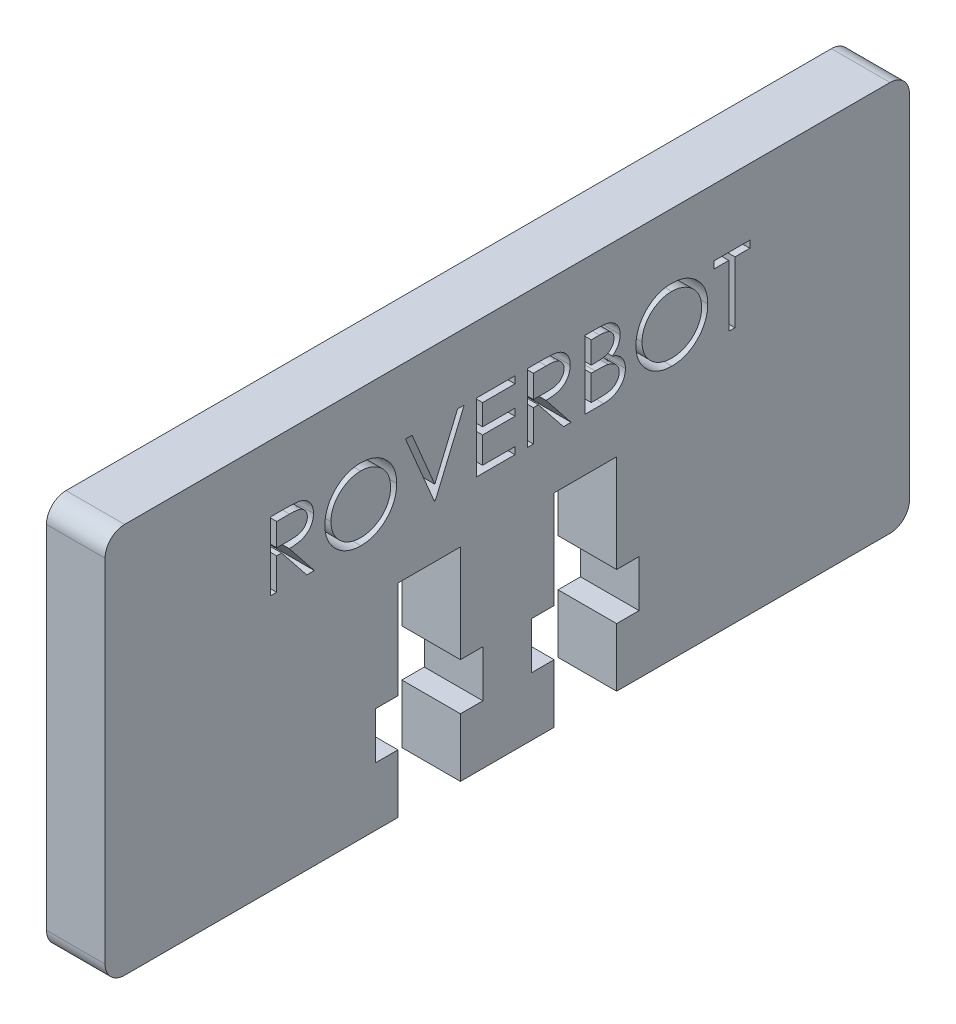
SolidWorks part; units mm, degrees
material "Beech"
ref_plane "Front Plane" through (0, 0, 0) normal (0, 0, 1) x (1, 0, 0)
ref_plane "Top Plane" through (0, 0, 0) normal (0, 1, 0) x (1, 0, 0)
ref_plane "Right Plane" through (0, 0, 0) normal (1, 0, 0) x (0, 0, -1)
sketch "Sketch1" plane through (0, 0, 0) normal (1, 0, 0) x (0, 0, -1)
  line L0 (-4, 0) -> (4, 0) construction
  line L1 (-5.6, 0) -> (-5.6, 3)
  line L2 (-5.6, 3) -> (-6.75, 3)
  line L3 (-6.75, 3) -> (-6.75, 5.4)
  line L4 (-6.75, 5.4) -> (-1.25, 5.4) construction
  line L5 (-1.25, 5.4) -> (-1.25, 3)
  line L6 (-1.25, 3) -> (-2.4, 3)
  line L7 (-2.4, 3) -> (-2.4, 0)
  line L8 (-2.4, 0) -> (2.4, 0)
  line L9 (2.4, 0) -> (2.4, 3)
  line L10 (2.4, 3) -> (1.25, 3)
  line L11 (1.25, 3) -> (1.25, 5.4)
  line L12 (1.25, 5.4) -> (6.75, 5.4) construction
  line L13 (6.75, 5.4) -> (6.75, 3)
  line L14 (6.75, 3) -> (5.6, 3)
  line L15 (5.6, 3) -> (5.6, 0)
  line L16 (5.6, 0) -> (20.6, 0)
  line L17 (-20.6, 0) -> (-20.6, 20)
  line L18 (-6.75, 5.4) -> (-5.6, 5.4)
  line L19 (-5.6, 5.4) -> (-5.6, 10.4)
  line L20 (-5.6, 10.4) -> (-2.4, 10.4)
  line L21 (-2.4, 10.4) -> (-2.4, 5.4)
  line L22 (-2.4, 5.4) -> (-1.25, 5.4)
  line L23 (1.25, 5.4) -> (2.4, 5.4)
  line L24 (2.4, 5.4) -> (2.4, 10.4)
  line L25 (2.4, 10.4) -> (5.6, 10.4)
  line L26 (5.6, 10.4) -> (5.6, 5.4)
  line L27 (5.6, 5.4) -> (6.75, 5.4)
  line L28 (-20.6, 20) -> (20.6, 20)
  line L29 (20.6, 20) -> (20.6, 0)
  line L30 (-20.6, 0) -> (-5.6, 0)
  point P3 (0, 0)
  point P10 (-4, 5.4)
  point P23 (4, 5.4)
  dimension "D1" = 8
  dimension "D2" = 5.5
  dimension "D3" = 3.2
  dimension "D4" = 3.2
  dimension "D5" = 2.4
  dimension "D6" = 3
  dimension "D7" = 5
  dimension "D8" = 20
  dimension "D9" = 15
extrude "Boss-Extrude1" add sketch "Sketch1" along normal blind 3
fillet "Fillet1" radius 1 4 edges at (1.5, 0, -20.6) (1.5, 20, -20.6) (1.5, 0, 20.6) (1.5, 20, 20.6)
sketch "Sketch2" plane through (3, 0, 0) normal (1, 0, 0) x (0, 0, -1)
  text T0 "ROVERBOT"
extrude "Cut-Extrude1" cut sketch "Sketch2" against normal through all
